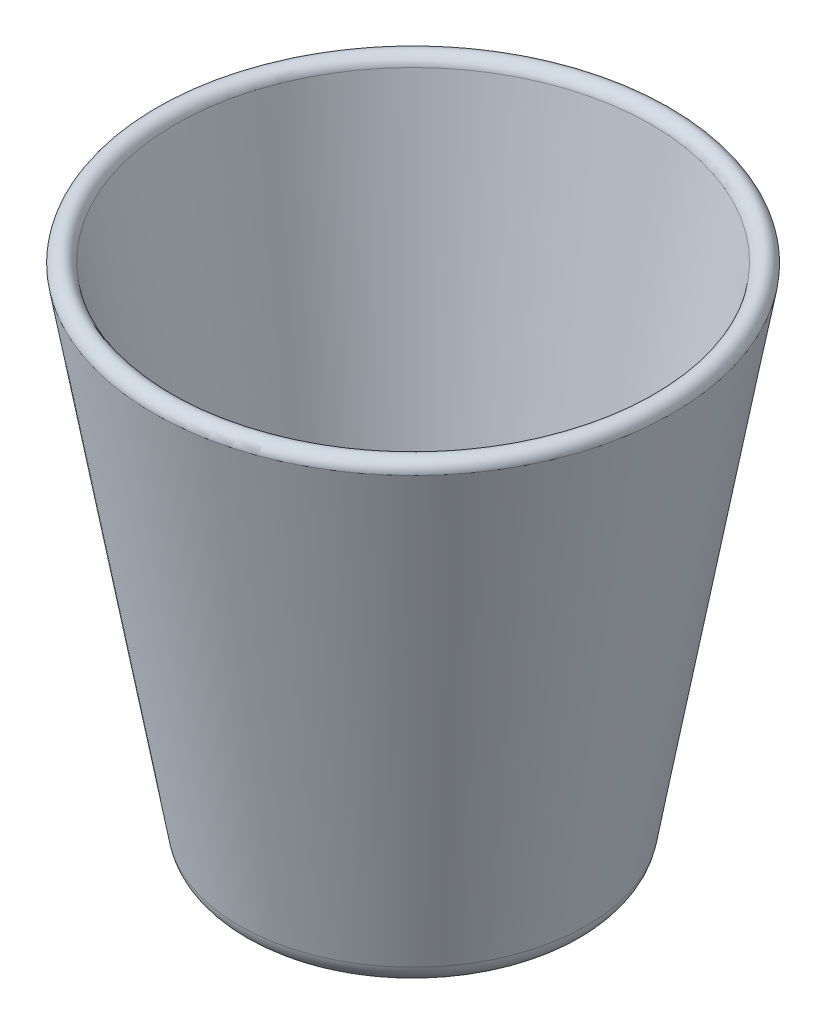
SolidWorks part; units mm, degrees
material "Ceramic Porcelain"
ref_plane "Front Plane" through (0, 0, 0) normal (0, 0, 1) x (1, 0, 0)
ref_plane "Top Plane" through (0, 0, 0) normal (0, 1, 0) x (1, 0, 0)
ref_plane "Right Plane" through (0, 0, 0) normal (1, 0, 0) x (0, 0, -1)
sketch "Sketch1" plane through (0, 0, 0) normal (0, 0, 1) x (1, 0, 0)
  line L0 (0, 0) -> (66.2095, 0)
  line L1 (77.9348, 9.8388) -> (116.5083, 228.6)
  line L2 (0, 0) -> (0, 198.0077) construction
  line L3 (76.2, 0) -> (76.2, 198.0077) construction
  line L4 (0, 9.525) -> (66.2095, 9.525)
  line L5 (68.5545, 11.4928) -> (106.9833, 229.4333)
  line L6 (0, 9.525) -> (0, 0)
  line L7 (68.5545, 11.4928) -> (107.1281, 230.254) construction
  line L8 (0, 9.525) -> (66.2095, 9.525) construction
  arc A0 (66.2095, 0) -> (77.9348, 9.8388) centre (66.2095, 11.9062) ccw
  arc A1 (106.9833, 229.4333) -> (116.5083, 228.6) centre (111.7094, 228.6) cw
  arc A2 (68.5545, 11.4928) -> (66.2095, 9.525) centre (66.2095, 11.9063) cw
  arc A3 (66.2095, 9.525) -> (68.5545, 11.4928) centre (66.2095, 11.9062) ccw construction
  dimension "Base Outer Radius" = 11.9063
  dimension "Base Inner Radius" = 2.3813
  dimension "Wall Height" = 228.6
  dimension "Wall Angle" = 10
  dimension "Base Dia" = 152.4
  dimension "Wall Thickness" = 9.525
revolve "Revolve1" add sketch "Sketch1" angle 360 about L2
equation "\"Wall Height@Sketch1\" = 1.5*\"Base Dia@Sketch1\""
equation "\"Base Outer Radius@Sketch1\" = 1.25*\"Wall Thickness@Sketch1\""
equation "\"Base Inner Radius@Sketch1\" = \"Base Outer Radius@Sketch1\" - \"Wall Thickness@Sketch1\""
equation "\"Wall Thickness@Sketch1\" = .0625 * \"Base Dia@Sketch1\""
